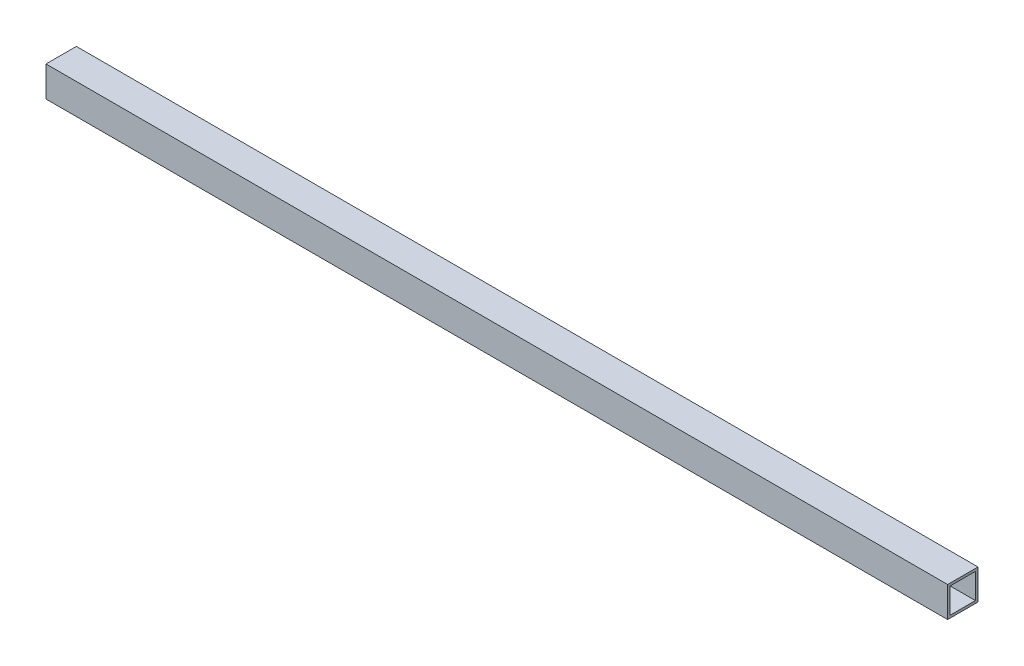
SolidWorks part; units mm, degrees
ref_plane "Alzado" through (0, 0, 0) normal (0, 0, 1) x (1, 0, 0)
ref_plane "Planta" through (0, 0, 0) normal (0, 1, 0) x (1, 0, 0)
ref_plane "Vista lateral" through (0, 0, 0) normal (1, 0, 0) x (0, 0, -1)
sketch "Croquis1" plane through (0, 0, 0) normal (1, 0, 0) x (0, 0, -1)
  line L0 (-7.9375, 7.9375) -> (-7.9375, -7.9375)
  line L1 (9.525, 9.525) -> (-9.525, 9.525)
  line L2 (9.525, 9.525) -> (9.525, -9.525)
  line L3 (9.525, -9.525) -> (-9.525, -9.525)
  line L4 (-9.525, 9.525) -> (-9.525, -9.525)
  line L5 (9.525, 9.525) -> (-9.525, -9.525) construction
  line L6 (9.525, -9.525) -> (-9.525, 9.525) construction
  line L7 (7.9375, -7.9375) -> (-7.9375, -7.9375)
  line L8 (7.9375, 7.9375) -> (7.9375, -7.9375)
  line L9 (7.9375, 7.9375) -> (-7.9375, 7.9375)
  point P0 (0, 0)
  dimension "D1" = 19.05
  dimension "D2" = 19.05
  dimension "D3" = 1.5875
extrude "Saliente-Extruir1" add sketch "Croquis1" along normal mid plane 565.15
